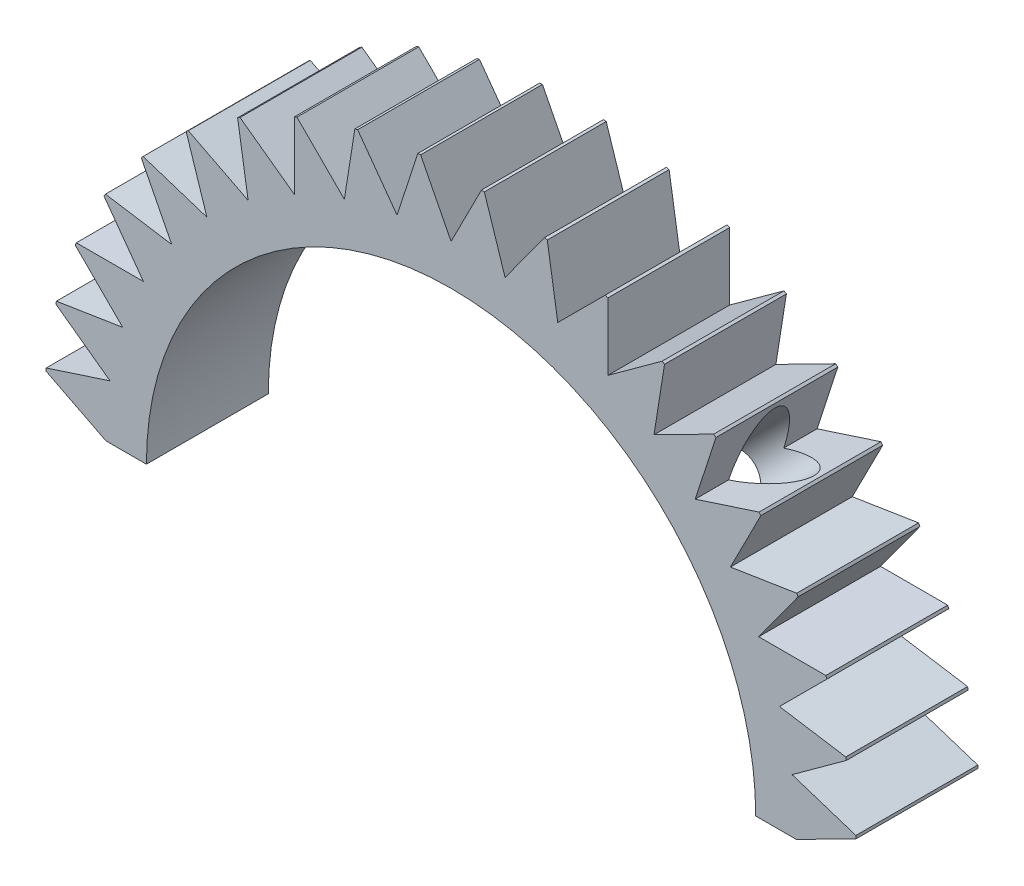
SolidWorks part; units mm, degrees
ref_plane "Front Plane" through (0, 0, 0) normal (0, 0, 1) x (1, 0, 0)
ref_plane "Top Plane" through (0, 0, 0) normal (0, 1, 0) x (1, 0, 0)
ref_plane "Right Plane" through (0, 0, 0) normal (1, 0, 0) x (0, 0, -1)
sketch "Sketch1" plane through (0, 0, 0) normal (0, 0, 1) x (1, 0, 0)
  line L3 (-50, 0) -> (-37.5, 0)
  line L6 (37.5, 0) -> (50, 0)
  arc A2 (37.5, 0) -> (-37.5, 0) centre (0, 0) ccw
  arc A3 (50, 0) -> (-50, 0) centre (0, 0) ccw
  dimension "D1" = 100
  dimension "D2" = 75
extrude "Boss-Extrude1" add sketch "Sketch1" along normal mid plane 15 contours A2 L3 A3 L6
ref_plane "Plane3" through (-26.5165, 26.5165, 0) normal (0.7071, -0.7071, 0) x (0, 0, -1)
ref_plane "Plane4" through (26.5165, 26.5165, 0) normal (-0.7071, -0.7071, 0) x (0, 0, -1)
sketch "Sketch2" plane through (0, 0, 0) normal (0, 0, 1) x (1, 0, 0)
  line L0 (-3.75, 49.8592) -> (0, 42.5)
  line L3 (0, 0) -> (0, 61.0696) construction
  line L4 (0, 42.5) -> (3.75, 49.8592)
  line L5 (4.0959, 49.832) -> (6.6485, 41.9768)
  line L6 (6.6485, 41.9768) -> (11.5035, 48.6587)
  line L7 (11.8409, 48.5777) -> (13.1332, 40.4199)
  line L8 (13.1332, 40.4199) -> (18.9738, 46.2601)
  line L9 (19.2943, 46.1273) -> (19.2946, 37.8678)
  line L10 (19.2946, 37.8678) -> (25.9769, 42.7224)
  line L11 (26.2727, 42.5411) -> (24.9809, 34.3832)
  line L12 (24.9809, 34.3832) -> (32.3403, 38.1327)
  line L13 (32.6041, 37.9074) -> (30.052, 30.052)
  line L14 (30.052, 30.052) -> (37.9074, 32.6041)
  line L15 (38.1327, 32.3403) -> (34.3832, 24.9809)
  line L16 (34.3832, 24.9809) -> (42.5411, 26.2727)
  line L17 (42.7224, 25.9769) -> (37.8678, 19.2946)
  line L18 (37.8678, 19.2946) -> (46.1273, 19.2943)
  line L19 (46.2601, 18.9738) -> (40.4199, 13.1332)
  line L20 (40.4199, 13.1332) -> (48.5777, 11.8409)
  line L21 (48.6587, 11.5035) -> (41.9768, 6.6485)
  line L22 (41.9768, 6.6485) -> (49.832, 4.0959)
  line L23 (49.8592, 3.75) -> (42.5, 0)
  line L24 (42.5, 0) -> (49.8592, -3.75)
  line L25 (49.832, -4.0959) -> (41.9768, -6.6485) [skipped]
  line L26 (41.9768, -6.6485) -> (48.6587, -11.5035) [skipped]
  line L27 (48.5777, -11.8409) -> (40.4199, -13.1332) [skipped]
  line L28 (40.4199, -13.1332) -> (46.2601, -18.9738) [skipped]
  line L29 (46.1273, -19.2943) -> (37.8678, -19.2946) [skipped]
  line L30 (37.8678, -19.2946) -> (42.7224, -25.9769) [skipped]
  line L31 (42.5411, -26.2727) -> (34.3832, -24.9809) [skipped]
  line L32 (34.3832, -24.9809) -> (38.1327, -32.3403) [skipped]
  line L33 (37.9074, -32.6041) -> (30.052, -30.052) [skipped]
  line L34 (30.052, -30.052) -> (32.6041, -37.9074) [skipped]
  line L35 (32.3403, -38.1327) -> (24.9809, -34.3832) [skipped]
  line L36 (24.9809, -34.3832) -> (26.2727, -42.5411) [skipped]
  line L37 (25.9769, -42.7224) -> (19.2946, -37.8678) [skipped]
  line L38 (19.2946, -37.8678) -> (19.2943, -46.1273) [skipped]
  line L39 (18.9738, -46.2601) -> (13.1332, -40.4199) [skipped]
  line L40 (13.1332, -40.4199) -> (11.8409, -48.5777) [skipped]
  line L41 (11.5035, -48.6587) -> (6.6485, -41.9768) [skipped]
  line L42 (6.6485, -41.9768) -> (4.0959, -49.832) [skipped]
  line L43 (3.75, -49.8592) -> (0, -42.5) [skipped]
  line L44 (0, -42.5) -> (-3.75, -49.8592) [skipped]
  line L45 (-4.0959, -49.832) -> (-6.6485, -41.9768) [skipped]
  line L46 (-6.6485, -41.9768) -> (-11.5035, -48.6587) [skipped]
  line L47 (-11.8409, -48.5777) -> (-13.1332, -40.4199) [skipped]
  line L48 (-13.1332, -40.4199) -> (-18.9738, -46.2601) [skipped]
  line L49 (-19.2943, -46.1273) -> (-19.2946, -37.8678) [skipped]
  line L50 (-19.2946, -37.8678) -> (-25.9769, -42.7224) [skipped]
  line L51 (-26.2727, -42.5411) -> (-24.9809, -34.3832) [skipped]
  line L52 (-24.9809, -34.3832) -> (-32.3403, -38.1327) [skipped]
  line L53 (-32.6041, -37.9074) -> (-30.052, -30.052) [skipped]
  line L54 (-30.052, -30.052) -> (-37.9074, -32.6041) [skipped]
  line L55 (-38.1327, -32.3403) -> (-34.3832, -24.9809) [skipped]
  line L56 (-34.3832, -24.9809) -> (-42.5411, -26.2727) [skipped]
  line L57 (-42.7224, -25.9769) -> (-37.8678, -19.2946) [skipped]
  line L58 (-37.8678, -19.2946) -> (-46.1273, -19.2943) [skipped]
  line L59 (-46.2601, -18.9738) -> (-40.4199, -13.1332) [skipped]
  line L60 (-40.4199, -13.1332) -> (-48.5777, -11.8409) [skipped]
  line L61 (-48.6587, -11.5035) -> (-41.9768, -6.6485) [skipped]
  line L62 (-41.9768, -6.6485) -> (-49.832, -4.0959) [skipped]
  line L63 (-49.8592, -3.75) -> (-42.5, 0)
  line L64 (-42.5, 0) -> (-49.8592, 3.75)
  line L65 (-49.832, 4.0959) -> (-41.9768, 6.6485)
  line L66 (-41.9768, 6.6485) -> (-48.6587, 11.5035)
  line L67 (-48.5777, 11.8409) -> (-40.4199, 13.1332)
  line L68 (-40.4199, 13.1332) -> (-46.2601, 18.9738)
  line L69 (-46.1273, 19.2943) -> (-37.8678, 19.2946)
  line L70 (-37.8678, 19.2946) -> (-42.7224, 25.9769)
  line L71 (-42.5411, 26.2727) -> (-34.3832, 24.9809)
  line L72 (-34.3832, 24.9809) -> (-38.1327, 32.3403)
  line L73 (-37.9074, 32.6041) -> (-30.052, 30.052)
  line L74 (-30.052, 30.052) -> (-32.6041, 37.9074)
  line L75 (-32.3403, 38.1327) -> (-24.9809, 34.3832)
  line L76 (-24.9809, 34.3832) -> (-26.2727, 42.5411)
  line L77 (-25.9769, 42.7224) -> (-19.2946, 37.8678)
  line L78 (-19.2946, 37.8678) -> (-19.2943, 46.1273)
  line L79 (-18.9738, 46.2601) -> (-13.1332, 40.4199)
  line L80 (-13.1332, 40.4199) -> (-11.8409, 48.5777)
  line L81 (-11.5035, 48.6587) -> (-6.6485, 41.9768)
  line L82 (-6.6485, 41.9768) -> (-4.0959, 49.832)
  arc A1 (50, 0) -> (-50, 0) centre (0, 0) ccw construction
  arc A2 (-3.75, 49.8592) -> (3.75, 49.8592) centre (0, 0) cw
  arc A3 (37.5, 0) -> (-37.5, 0) centre (0, 0) ccw construction
  arc A4 (4.0959, 49.832) -> (11.5035, 48.6587) centre (0, 0) cw
  arc A5 (11.8409, 48.5777) -> (18.9738, 46.2601) centre (0, 0) cw
  arc A6 (19.2943, 46.1273) -> (25.9769, 42.7224) centre (0, 0) cw
  arc A7 (26.2727, 42.5411) -> (32.3403, 38.1327) centre (0, 0) cw
  arc A8 (32.6041, 37.9074) -> (37.9074, 32.6041) centre (0, 0) cw
  arc A9 (38.1327, 32.3403) -> (42.5411, 26.2727) centre (0, 0) cw
  arc A10 (42.7224, 25.9769) -> (46.1273, 19.2943) centre (0, 0) cw
  arc A11 (46.2601, 18.9738) -> (48.5777, 11.8409) centre (0, 0) cw
  arc A12 (48.6587, 11.5035) -> (49.832, 4.0959) centre (0, 0) cw
  arc A13 (49.8592, 3.75) -> (49.8592, -3.75) centre (0, 0) cw
  arc A14 (49.832, -4.0959) -> (48.6587, -11.5035) centre (0, 0) cw [skipped]
  arc A15 (48.5777, -11.8409) -> (46.2601, -18.9738) centre (0, 0) cw [skipped]
  arc A16 (46.1273, -19.2943) -> (42.7224, -25.9769) centre (0, 0) cw [skipped]
  arc A17 (42.5411, -26.2727) -> (38.1327, -32.3403) centre (0, 0) cw [skipped]
  arc A18 (37.9074, -32.6041) -> (32.6041, -37.9074) centre (0, 0) cw [skipped]
  arc A19 (32.3403, -38.1327) -> (26.2727, -42.5411) centre (0, 0) cw [skipped]
  arc A20 (25.9769, -42.7224) -> (19.2943, -46.1273) centre (0, 0) cw [skipped]
  arc A21 (18.9738, -46.2601) -> (11.8409, -48.5777) centre (0, 0) cw [skipped]
  arc A22 (11.5035, -48.6587) -> (4.0959, -49.832) centre (0, 0) cw [skipped]
  arc A23 (3.75, -49.8592) -> (-3.75, -49.8592) centre (0, 0) cw [skipped]
  arc A24 (-4.0959, -49.832) -> (-11.5035, -48.6587) centre (0, 0) cw [skipped]
  arc A25 (-11.8409, -48.5777) -> (-18.9738, -46.2601) centre (0, 0) cw [skipped]
  arc A26 (-19.2943, -46.1273) -> (-25.9769, -42.7224) centre (0, 0) cw [skipped]
  arc A27 (-26.2727, -42.5411) -> (-32.3403, -38.1327) centre (0, 0) cw [skipped]
  arc A28 (-32.6041, -37.9074) -> (-37.9074, -32.6041) centre (0, 0) cw [skipped]
  arc A29 (-38.1327, -32.3403) -> (-42.5411, -26.2727) centre (0, 0) cw [skipped]
  arc A30 (-42.7224, -25.9769) -> (-46.1273, -19.2943) centre (0, 0) cw [skipped]
  arc A31 (-46.2601, -18.9738) -> (-48.5777, -11.8409) centre (0, 0) cw [skipped]
  arc A32 (-48.6587, -11.5035) -> (-49.832, -4.0959) centre (0, 0) cw [skipped]
  arc A33 (-49.8592, -3.75) -> (-49.8592, 3.75) centre (0, 0) cw
  arc A34 (-49.832, 4.0959) -> (-48.6587, 11.5035) centre (0, 0) cw
  arc A35 (-48.5777, 11.8409) -> (-46.2601, 18.9738) centre (0, 0) cw
  arc A36 (-46.1273, 19.2943) -> (-42.7224, 25.9769) centre (0, 0) cw
  arc A37 (-42.5411, 26.2727) -> (-38.1327, 32.3403) centre (0, 0) cw
  arc A38 (-37.9074, 32.6041) -> (-32.6041, 37.9074) centre (0, 0) cw
  arc A39 (-32.3403, 38.1327) -> (-26.2727, 42.5411) centre (0, 0) cw
  arc A40 (-25.9769, 42.7224) -> (-19.2943, 46.1273) centre (0, 0) cw
  arc A41 (-18.9738, 46.2601) -> (-11.8409, 48.5777) centre (0, 0) cw
  arc A42 (-11.5035, 48.6587) -> (-4.0959, 49.832) centre (0, 0) cw
  point P13 (0, 37.5)
  point P134 (0, 0)
  dimension "D1" = 3.75
  dimension "D2" = 3.75
  dimension "D3" = 5
  dimension "D4" = 40
extrude "Cut-Extrude1" cut sketch "Sketch2" against normal mid plane 15
ref_plane "Plane5" through (-19.4454, 19.4454, 0) normal (0.7071, -0.7071, 0) x (0, 0, -1)
ref_plane "Plane6" through (19.4454, 19.4454, 0) normal (-0.7071, -0.7071, 0) x (0, 0, -1)
hole_wizard "M8x1.25 Tapped Hole4" positions "Sketch15" profile "Sketch16" tap size "M8x1.25" standard "ANSI Metric" end condition through all
sketch "Sketch15" plane through (-19.4454, 19.4454, 0) normal (0.7071, -0.7071, 0) x (0, 0, -1)
  point P0 (0, 0)
sketch "Sketch16" plane through (-19.4454, 19.4454, 0) normal (0, 0, 1) x (0.7071, 0.7071, 0)
  line L0 (0, 0) -> (0, 43.0115)
  line L1 (0, 43.0115) -> (3.4, 43.0115)
  line L2 (3.4, 43.0115) -> (3.4, 0)
  line L5 (3.4, 0) -> (0, 0)
  line L11 (0, -6.35) -> (0, 107.95) construction
  dimension "Thru Tap Drill Dia." = 6.8
  dimension "Thru Tap Drill Depth" = 43.0115
cosmetic thread "Hole Thread1" parameters "D2"=8
hole_wizard "M8x1.25 Tapped Hole5" positions "Sketch17" profile "Sketch18" tap size "M8x1.25" standard "ANSI Metric" end condition through all
sketch "Sketch17" plane through (19.4454, 19.4454, 0) normal (-0.7071, -0.7071, 0) x (0, 0, -1)
  point P0 (0, 0)
sketch "Sketch18" plane through (19.4454, 19.4454, 0) normal (0, 0, 1) x (0.7071, -0.7071, 0)
  line L0 (0, 0) -> (0, 43.0115)
  line L1 (0, 43.0115) -> (3.4, 43.0115)
  line L2 (3.4, 43.0115) -> (3.4, 0)
  line L5 (3.4, 0) -> (0, 0)
  line L11 (0, -6.35) -> (0, 107.95) construction
  dimension "Thru Tap Drill Dia." = 6.8
  dimension "Thru Tap Drill Depth" = 43.0115
cosmetic thread "Hole Thread2" parameters "D2"=8
